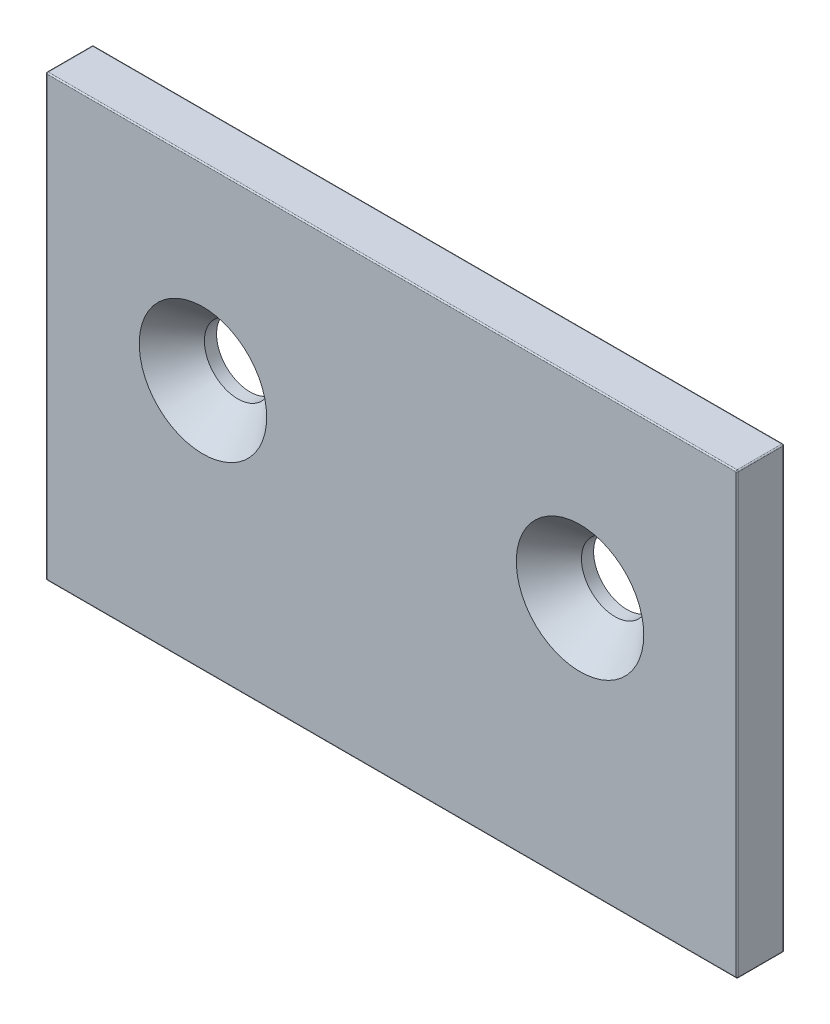
SolidWorks part; units mm, degrees
ref_plane "Front Plane" through (0, 0, 0) normal (0, 0, 1) x (1, 0, 0)
ref_plane "Top Plane" through (0, 0, 0) normal (0, 1, 0) x (1, 0, 0)
ref_plane "Right Plane" through (0, 0, 0) normal (1, 0, 0) x (0, 0, -1)
sketch "Sketch1" plane through (0, 0, 0) normal (0, 0, 1) x (1, 0, 0)
  line L1 (34.925, 0) -> (-34.925, 0)
  line L2 (34.925, 0) -> (34.925, 44.45)
  line L3 (34.925, 44.45) -> (-34.925, 44.45)
  line L4 (-34.925, 0) -> (-34.925, 44.45)
  dimension "D1" = 69.85
  dimension "D2" = 44.45
extrude "Boss-Extrude1" add sketch "Sketch1" along normal blind 4.7498 contours L4 L3 L2 L1
hole_wizard "CSK for 1/4 Flat Head Machine Screw1" positions "Sketch3" profile "Sketch4" countersink size "1/4" standard "ANSI Inch" end condition through all
sketch "Sketch3" plane through (0, 0, 4.7498) normal (0, 0, 1) x (1, 0, 0)
  line L0 (0, 0) -> (0, 25.4) construction
  point P7 (-19.05, 25.4)
  point P9 (19.05, 25.4)
  point P12 (0, 0)
  point P13 (0, 0)
  dimension "D1" = 25.4
  dimension "D2" = 38.1
sketch "Sketch4" plane through (19.05, 25.4, 4.7498) normal (1, 0, 0) x (0, -1, 0)
  line L0 (0, 0) -> (0, 4.7498)
  line L1 (0, 4.7498) -> (3.3782, 4.7498)
  line L2 (3.3782, 4.7498) -> (3.3782, 3.5209)
  line L3 (3.3782, 3.5209) -> (6.4389, 0)
  line L5 (6.4389, 0) -> (0, 0)
  line L6 (-3.3782, 3.5209) -> (-6.4389, 0) construction
  line L11 (0, -6.35) -> (0, 107.95) construction
  dimension "Thru Hole Dia." = 6.7564
  dimension "Thru Hole Depth" = 4.7498
  dimension "Near C'Sink Dia." = 12.8778
  dimension "Near C'Sink Angle" = 82
fillet "Fillet1" radius 0.127 12 edges at (0, 0, 4.7498) (0, 0, 0) (-34.925, 22.225, 4.7498) (-34.925, 0, 2.3749) (-34.925, 22.225, 0) (0, 44.45, 4.7498) (-34.925, 44.45, 2.3749) (0, 44.45, 0) (34.925, 0, 2.3749) (34.925, 22.225, 4.7498) (34.925, 44.45, 2.3749) (34.925, 22.225, 0)
